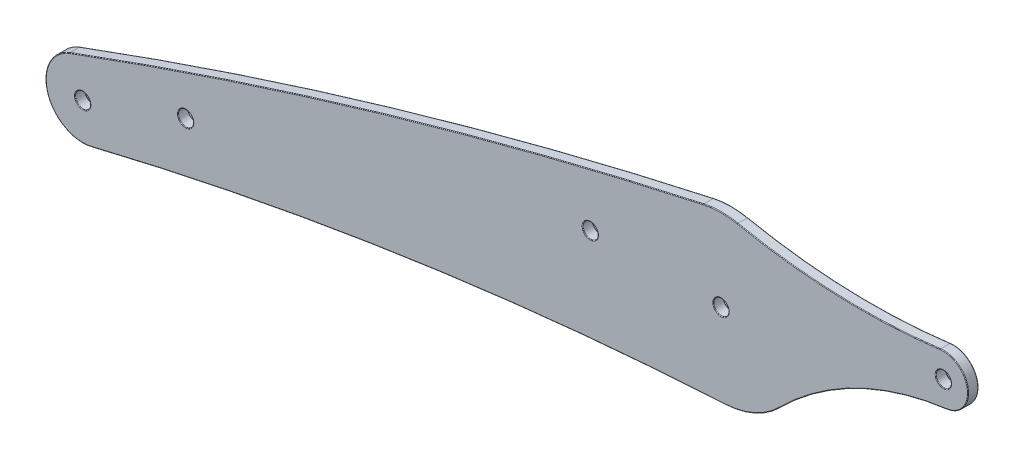
SolidWorks part; units mm, degrees
ref_plane "Front Plane" through (0, 0, 0) normal (0, 0, 1) x (1, 0, 0)
ref_plane "Top Plane" through (0, 0, 0) normal (0, 1, 0) x (1, 0, 0)
ref_plane "Right Plane" through (0, 0, 0) normal (1, 0, 0) x (0, 0, -1)
sketch "Sketch1" plane through (0, 0, 0) normal (0, 0, 1) x (1, 0, 0)
  line L0 (-207.5594, 167.9915) -> (1.4673, 213.8589) construction
  line L1 (-207.5594, 167.9915) -> (1.4673, 213.8589) construction
  circle A0 centre (-207.5594, 167.9915) radius 9 construction
  circle A1 centre (-52.5327, 202.0095) radius 10 construction
  circle A2 centre (-52.5327, 202.0095) radius 20 construction
  circle A3 centre (1.4673, 213.8589) radius 6 construction
  arc A4 (-210.6876, 176.4304) -> (-56.8079, 221.5472) centre (189.0196, -901.8711) cw
  arc A5 (-48.5315, 221.6052) -> (0.6985, 219.8095) centre (-18.5228, 368.5728) ccw
  arc A6 (-205.4319, 159.2466) -> (-51.4286, 182.04) centre (-4.5037, -666.6637) cw
  arc A7 (-38.3644, 187.8936) -> (2.2376, 207.9086) centre (11.2247, 138.4879) cw
  arc A8 (-56.8079, 221.5472) -> (-48.5315, 221.6052) centre (-52.5327, 202.0095) cw
  arc A9 (-51.4286, 182.04) -> (-38.3644, 187.8936) centre (-52.5327, 202.0095) ccw
  arc A10 (0.6985, 219.8095) -> (2.2376, 207.9086) centre (1.4673, 213.8589) cw
  arc A11 (-210.6876, 176.4304) -> (-205.4319, 159.2466) centre (-207.5594, 167.9915) ccw
  arc A12 (-207.5594, 167.9915) -> (1.4673, 213.8589) centre (64.7172, -573.605) cw construction
  point P2 (-52.5327, 202.0095)
  point P24 (-182.5594, 176.6978)
  point P27 (-84.2827, 202.2165)
  dimension "D1" = 18
  dimension "D2" = 20
  dimension "D3" = 40
  dimension "D4" = 12
  dimension "D5" = 850
  dimension "D6" = 1150
  dimension "D7" = 70
  dimension "D8" = 150
  dimension "D9" = 790
  dimension "D10" = 31.75
  dimension "D11" = 25
extrude "Boss-Extrude1" add sketch "Sketch1" against normal blind 2.5
hole_wizard "M3.5 Clearance Hole1" positions "Sketch2" profile "Sketch3" hole size "M3.5" standard "ISO" end condition through all
sketch "Sketch2" plane through (0, 0, 0) normal (0, 0, 1) x (1, 0, 0)
  point P0 (-207.5594, 167.9915)
  point P3 (-182.5594, 176.6978)
  point P6 (-84.2827, 202.2165)
  point P9 (-52.5327, 202.0095)
  point P12 (1.4673, 213.8589)
sketch "Sketch3" plane through (-207.5594, 167.9915, 0) normal (1, 0, 0) x (0, -1, 0)
  line L0 (0, 0) -> (0, 2.5)
  line L1 (0, 2.5) -> (1.85, 2.5)
  line L2 (1.85, 2.5) -> (1.85, 0)
  line L5 (1.85, 0) -> (0, 0)
  line L11 (0, -6.35) -> (0, 107.95) construction
  dimension "Thru Hole Dia." = 3.7
  dimension "Thru Hole Depth" = 2.5
fillet "Fillet1" radius 0.15 26 edges at (-128.9532, 174.1765, -2.5) (-44.3548, 183.7579, -2.5) (-19.7259, 201.2737, -2.5) (7.4178, 214.6285, -2.5) (-23.9907, 218.6725, -2.5) (-52.6728, 222.009, -2.5) (-134.5351, 201.6742, -2.5) (-216.1659, 165.3593, -2.5) (3.3173, 213.8589, -2.5) (-50.6827, 202.0095, -2.5) (-82.4327, 202.2165, -2.5) (-180.7094, 176.6978, -2.5) (-205.7094, 167.9915, -2.5) (-134.5351, 201.6742, 0) (-52.6728, 222.009, 0) (-23.9907, 218.6725, 0) (7.4178, 214.6285, 0) (-19.7259, 201.2737, 0) (-44.3548, 183.7579, 0) (-128.9532, 174.1765, 0) (-216.1659, 165.3593, 0) (3.3173, 213.8589, 0) (-50.6827, 202.0095, 0) (-82.4327, 202.2165, 0) (-180.7094, 176.6978, 0) (-205.7094, 167.9915, 0)
